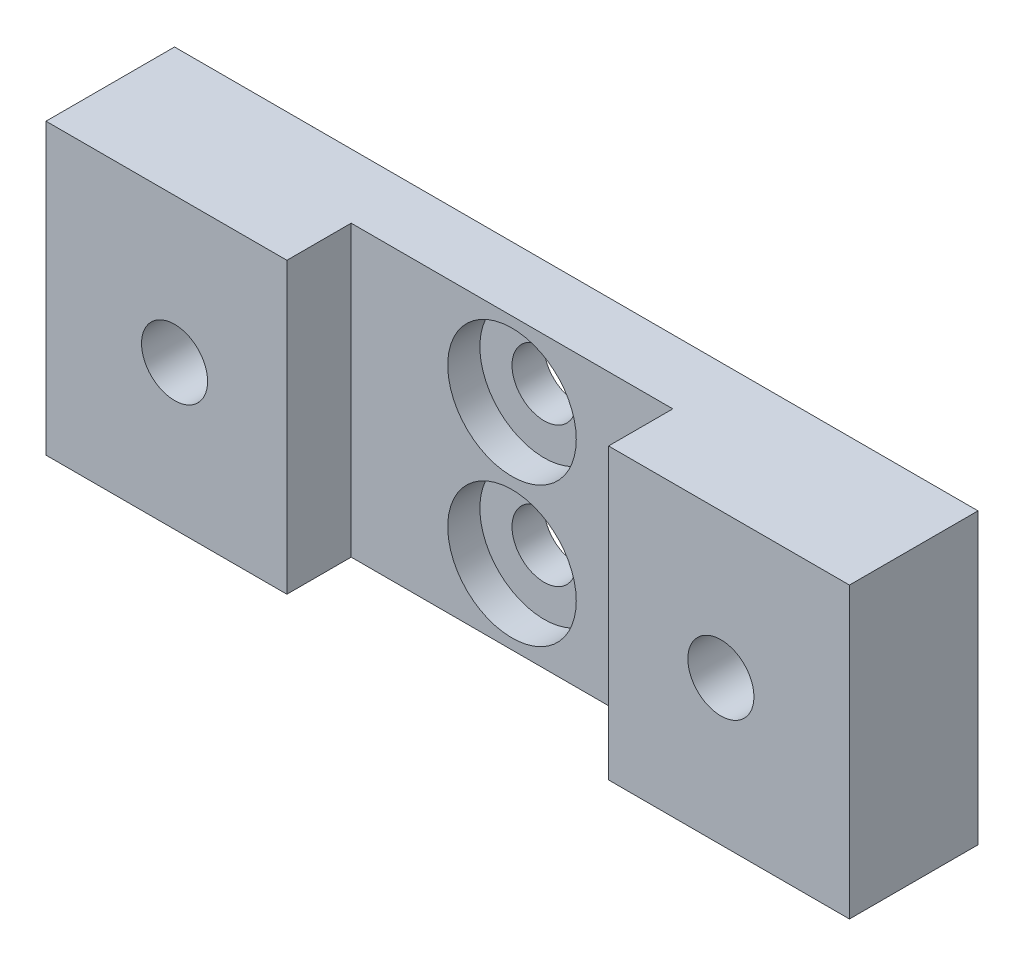
SolidWorks part; units mm, degrees
ref_plane "Front Plane" through (0, 0, 0) normal (0, 0, 1) x (1, 0, 0)
ref_plane "Top Plane" through (0, 0, 0) normal (0, 1, 0) x (1, 0, 0)
ref_plane "Right Plane" through (0, 0, 0) normal (1, 0, 0) x (0, 0, -1)
sketch "Sketch1" plane through (0, 0, 0) normal (0, 1, 0) x (1, 0, 0)
  line L0 (-39.6875, 0) -> (39.6875, 0)
  line L1 (39.6875, 0) -> (39.6875, -12.7)
  line L2 (39.6875, -12.7) -> (15.8877, -12.7)
  line L3 (15.8877, -12.7) -> (15.8877, -6.35)
  line L4 (15.8877, -6.35) -> (-15.8877, -6.35)
  line L5 (-15.8877, -6.35) -> (-15.8877, -12.7)
  line L6 (-15.8877, -12.7) -> (-39.6875, -12.7)
  line L7 (-39.6875, -12.7) -> (-39.6875, 0)
  point P7 (0, 0)
  point P10 (0, -6.35)
  dimension "D1" = 79.375
  dimension "D2" = 12.7
  dimension "D3" = 31.7754
  dimension "D4" = 6.35
extrude "Boss-Extrude1" add sketch "Sketch1" along normal blind 28.575
hole_wizard "Hole1" positions "Sketch2" profile "Sketch3" legacy end condition through all
sketch "Sketch2" plane through (0, 0, 6.35) normal (0, 0, -1) x (-1, 0, 0)
  line L3 (0, 21.1963) -> (0, 7.3787) construction
  point P0 (0, 7.3787)
  point P2 (0, 21.1963)
  point P37 (0, 14.2875)
  dimension "D1" = 13.8176
  dimension "D2" = 21.1963
sketch "Sketch3" plane through (0, 7.3787, 6.35) normal (1, 0, 0) x (0, -1, 0)
  line L0 (0, 0) -> (0, 8.2577)
  line L1 (0, 8.2577) -> (3.175, 6.35)
  line L2 (3.175, 6.35) -> (3.175, 3.175)
  line L3 (3.175, 3.175) -> (6.35, 3.175)
  line L4 (6.35, 0) -> (0, 0)
  line L5 (0, -11.3109) -> (0, 121.1557) construction
  line L6 (0, 8.2577) -> (-3.175, 6.35) construction
  line L7 (6.35, 3.175) -> (6.35, 0)
  line L8 (-24.3061, 15.5437) -> (-12.3224, 15.5437) construction
  dimension "Depth" = 6.35
  dimension "Drill Angle" = 118
  dimension "Diameter" = 6.35
  dimension "C-Bore Diameter" = 6.35
  dimension "C-Bore Depth" = 3.175
hole_wizard "5/16-18 Tapped Hole1" positions "Sketch6" profile "Sketch5" tap size "5/16-18" standard "ANSI Inch" end condition through all
sketch "Sketch6" plane through (0, 0, 12.7) normal (0, 0, 1) x (1, 0, 0)
  line L0 (-39.6875, 28.575) -> (-39.6875, 0) construction
  line L3 (39.6875, 28.575) -> (39.6875, 0) construction
  point P0 (-26.9875, 14.2875)
  point P2 (26.9875, 14.2875)
  point P8 (-39.6875, 14.2875)
  point P20 (39.6875, 14.2875)
  dimension "D1" = 12.7
  dimension "D2" = 12.7
sketch "Sketch5" plane through (-26.9875, 14.2875, 12.7) normal (1, 0, 0) x (0, -1, 0)
  line L0 (0, 0) -> (0, 12.7)
  line L1 (0, 12.7) -> (3.2639, 12.7)
  line L2 (3.2639, 12.7) -> (3.2639, 0)
  line L5 (3.2639, 0) -> (0, 0)
  line L11 (0, -6.35) -> (0, 107.95) construction
  dimension "Thru Tap Drill Dia." = 6.5278
  dimension "Thru Tap Drill Depth" = 12.7
cosmetic thread "Hole Thread1" parameters "D2"=7.9375
cosmetic thread "Hole Thread2" parameters "D2"=7.9375
